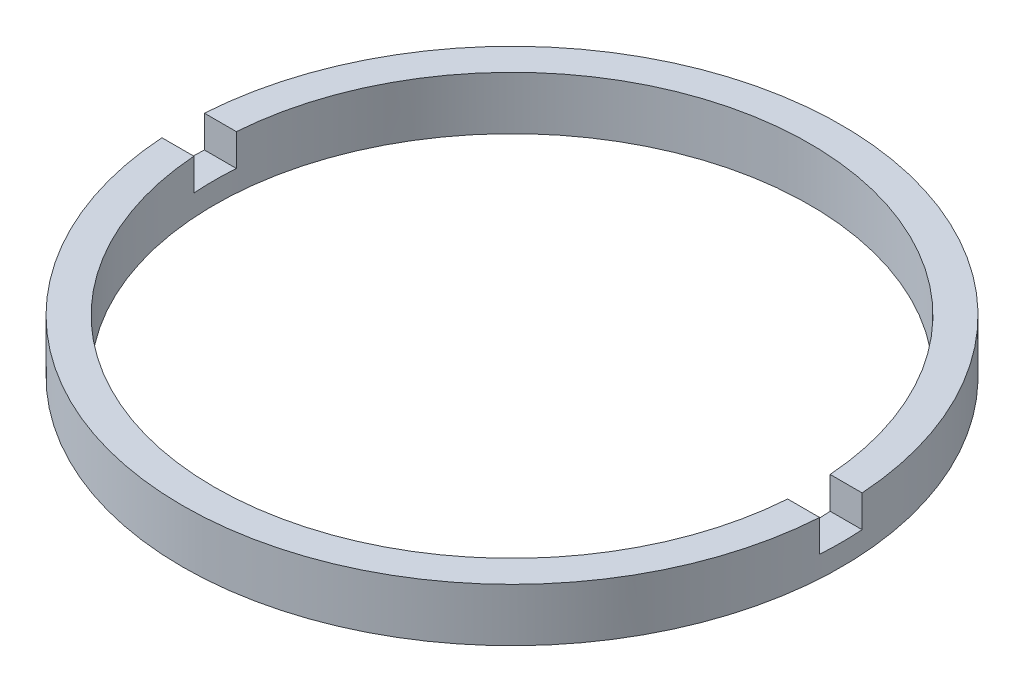
SolidWorks part; units mm, degrees
ref_plane "前视基准面" through (0, 0, 0) normal (0, 0, 1) x (1, 0, 0)
ref_plane "上视基准面" through (0, 0, 0) normal (0, 1, 0) x (1, 0, 0)
ref_plane "右视基准面" through (0, 0, 0) normal (1, 0, 0) x (0, 0, -1)
sketch "草图1" plane through (0, 0, 0) normal (0, 0, 1) x (1, 0, 0)
  line L0 (0, 56.2608) -> (0, -99.1922) construction
  line L1 (14, -1.9642) -> (15.5, -1.9642)
  line L4 (15.5, -1.9642) -> (15.5, -4.4642)
  line L5 (14, -4.4642) -> (14, -1.9642)
  line L7 (14, -4.4642) -> (15.5, -4.4642)
  dimension "D1" = 2.5
  dimension "D2" = 15.5
  dimension "D3" = 14
revolve "旋转1" add sketch "草图1" angle 360 about L0
cosmetic thread "装饰螺纹线1" parameters "D2"=30.9
sketch "草图2" plane through (0, -1.9642, 0) normal (0, 1, 0) x (1, 0, 0)
  line L0 (-28.67, 0) -> (29.9422, 0) construction
  line L2 (-26.8525, 1) -> (26.8525, 1)
  line L3 (-26.8525, 1) -> (-26.8525, -1)
  line L4 (-26.8525, -1) -> (26.8525, -1)
  line L5 (26.8525, 1) -> (26.8525, -1)
  line L6 (-26.8525, 1) -> (26.8525, -1) construction
  line L7 (-26.8525, -1) -> (26.8525, 1) construction
  point P3 (0, 0)
  dimension "D1" = 2
extrude "切除-拉伸1" cut sketch "草图2" against normal blind 1.5
